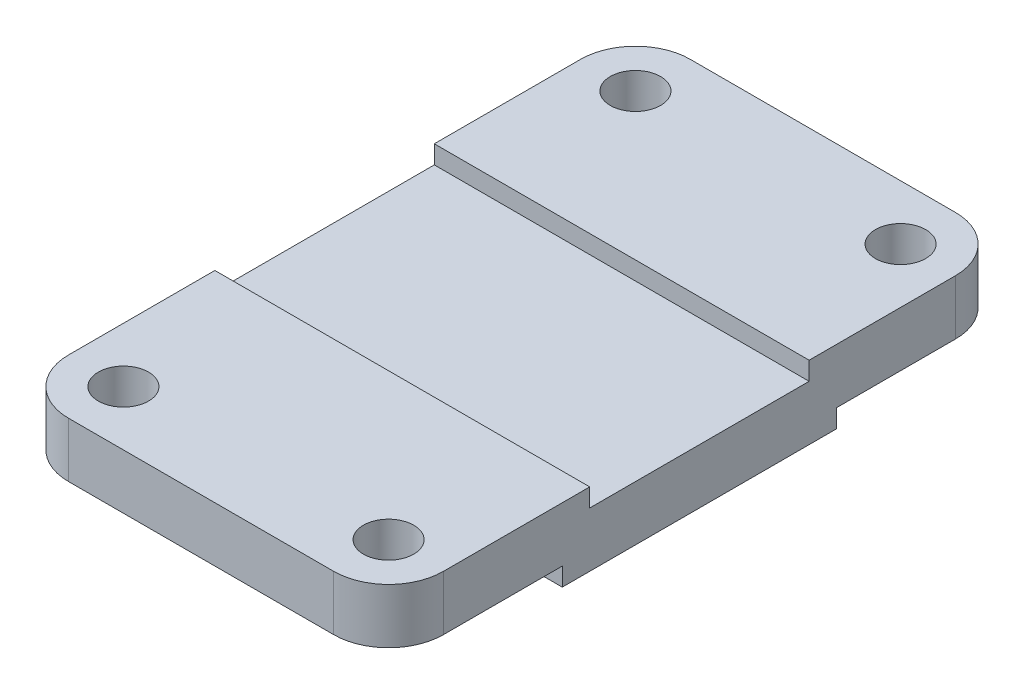
SolidWorks part; units mm, degrees
ref_plane "Alzado" through (0, 0, 0) normal (0, 0, 1) x (1, 0, 0)
ref_plane "Planta" through (0, 0, 0) normal (0, 1, 0) x (1, 0, 0)
ref_plane "Vista lateral" through (0, 0, 0) normal (1, 0, 0) x (0, 0, -1)
sketch "Croquis1" plane through (0, 0, 0) normal (0, 1, 0) x (1, 0, 0)
  line L1 (-29, 68) -> (29, 68)
  line L2 (-41, 56) -> (-41, -56)
  line L3 (-29, -68) -> (29, -68)
  line L4 (41, 56) -> (41, -56)
  line L5 (-41, 68) -> (41, -68) construction
  line L6 (-41, -68) -> (41, 68) construction
  arc A0 (-29, 68) -> (-41, 56) centre (-29, 56) ccw
  arc A1 (29, 68) -> (41, 56) centre (29, 56) cw
  arc A2 (-41, -56) -> (-29, -68) centre (-29, -56) ccw
  arc A3 (29, -68) -> (41, -56) centre (29, -56) ccw
  point P0 (0, 0)
  dimension "D1" = 12
  dimension "D2" = 12
  dimension "D3" = 12
  dimension "D4" = 12
  dimension "D5" = 82
  dimension "D6" = 136
extrude "Saliente-Extruir3" add sketch "Croquis1" along normal blind 16
sketch "Croquis6" plane through (0, 16, 0) normal (0, 1, 0) x (1, 0, 0)
  line L5 (0, 0) -> (11.5678, 0)
  line L6 (0, 0) -> (0, 10.904)
  circle A0 centre (29, 56) radius 5.5
  circle A1 centre (-29, 56) radius 5.5
  circle A2 centre (29, -56) radius 5.5
  circle A3 centre (-29, -56) radius 5.5
extrude "Cortar-Extruir3" cut sketch "Croquis6" against normal through all contours A1 | A0 | A3 | A2
sketch "Croquis7" plane through (-41, 0, 0) normal (-1, 0, 0) x (0, 0, 1)
  line L0 (0, 16) -> (-38, 16)
  line L1 (-56, 16) -> (56, 16) construction
  line L2 (0, 16) -> (38, 16)
  line L3 (-38, 16) -> (-38, 12)
  line L4 (38, 12) -> (38, 16)
  line L5 (-38, 12) -> (38, 12)
extrude "Cortar-Extruir4" cut sketch "Croquis7" against normal through all
sketch "Croquis8" plane through (-41, 0, 0) normal (-1, 0, 0) x (0, 0, 1)
  line L0 (38, 0) -> (68, 0)
  line L1 (-56, 0) -> (56, 0) construction
  line L2 (68, 0) -> (68, 4)
  line L3 (38, 0) -> (38, 4)
  line L4 (38, 4) -> (68, 4)
  line L5 (0, 0) -> (0, 12)
  line L6 (-38, 12) -> (38, 12) construction
  line L7 (-68, 0) -> (-68, 4)
  line L8 (-38, 0) -> (-68, 0)
  line L9 (-38, 0) -> (-38, 4)
  line L10 (-38, 4) -> (-68, 4)
  line M11 (-56, 16) -> (-56, 0)
  line M12 (-56, 0) -> (56, 0)
  line M13 (56, 0) -> (56, 16)
extrude "Cortar-Extruir5" cut sketch "Croquis8" against normal through all contours L9 L10 M11 M12 | L10 L7 L8 M11 | L4 L3 M12 M13 | L4 L0 L2 M13
sketch "Croquis9" plane through (-41, 0, 0) normal (-1, 0, 0) x (0, 0, 1)
  line L0 (-68, 16) -> (-68, 4) construction
  line L1 (-68, 16) -> (-68, 4)
  line L2 (68, 16) -> (68, 4) construction
  line L3 (68, 16) -> (68, 4)
  line L4 (-38, 0) -> (-38, 4) construction
  line L5 (-38, 0) -> (-38, 4)
  line L6 (38, 0) -> (38, 4) construction
  line L7 (38, 0) -> (38, 4)
  line L8 (-38, 4) -> (-30, 4)
  line L9 (-30, 4) -> (-30, 0)
  line L10 (-38, 0) -> (38, 0) construction
  line L11 (-30, 0) -> (-38, 0)
  line L12 (38, 4) -> (30, 4)
  line L13 (30, 4) -> (30, 0)
  line L14 (30, 0) -> (38, 0)
  line M8 (-38, 0) -> (38, 0)
  line M9 (38, 0) -> (38, 4)
extrude "Cortar-Extruir6" cut sketch "Croquis9" against normal through all contours L12 L13 M8 M9 | L11 L5 L8 L9
sketch "Croquis10" plane through (-41, 0, 0) normal (-1, 0, 0) x (0, 0, 1)
  line L0 (-68, 16) -> (-68, 4) construction
  line L1 (68, 16) -> (68, 4) construction
  line L2 (38, 12) -> (38, 16) construction
  line L3 (-38, 16) -> (-38, 12) construction
  line L4 (68, 16) -> (68, 4)
  line L5 (38, 12) -> (38, 16)
  line L6 (-38, 16) -> (-38, 12)
  line L7 (-68, 16) -> (-68, 4)
  line L8 (-38, 16) -> (-31, 16)
  line L9 (-31, 12) -> (-38, 12)
  line L10 (-38, 12) -> (38, 12) construction
  line L11 (-31, 12) -> (-31, 16)
  line L12 (38, 16) -> (31, 16)
  line L13 (31, 16) -> (31, 12)
  line L14 (31, 12) -> (38, 12)
  line M13 (38, 16) -> (38, 12)
  line M14 (38, 12) -> (-38, 12)
  line M15 (-38, 12) -> (-38, 16)
extrude "Saliente-Extruir4" add sketch "Croquis10" against normal blind 82 contours L11 L8 M14 M15 | L12 L13 M14 M13
sketch "Croquis11" plane through (-41, 0, 0) normal (-1, 0, 0) x (0, 0, 1)
  line L0 (-30, 4) -> (-30, 0) construction
  line L1 (-31, 12) -> (-31, 16) construction
  line L2 (31, 16) -> (31, 12) construction
  line L3 (30, 4) -> (30, 0) construction
  line L4 (68, 16) -> (68, 4) construction
  line L5 (-68, 16) -> (-68, 4) construction
  line L6 (-31, 12) -> (-31, 16)
  line L7 (31, 16) -> (31, 12)
  line L8 (30, 4) -> (30, 0)
  line L9 (68, 16) -> (68, 4)
  line L10 (-68, 16) -> (-68, 4)
  line L11 (-30, 4) -> (-30, 0)
  line L12 (-31, 16) -> (-24, 16)
  line L13 (-24, 16) -> (-24, 12)
  line L14 (-31, 12) -> (31, 12) construction
  line L15 (-24, 12) -> (-31, 12)
  line L16 (31, 16) -> (24, 16)
  line L17 (24, 16) -> (24, 12)
  line L18 (24, 12) -> (31, 12)
  line M6 (31, 16) -> (31, 12)
  line M7 (31, 12) -> (-31, 12)
  line M8 (-31, 12) -> (-31, 16)
extrude "Saliente-Extruir5" add sketch "Croquis11" against normal blind 82 contours L13 L12 M8 M7 | L16 L17 M7 M6
